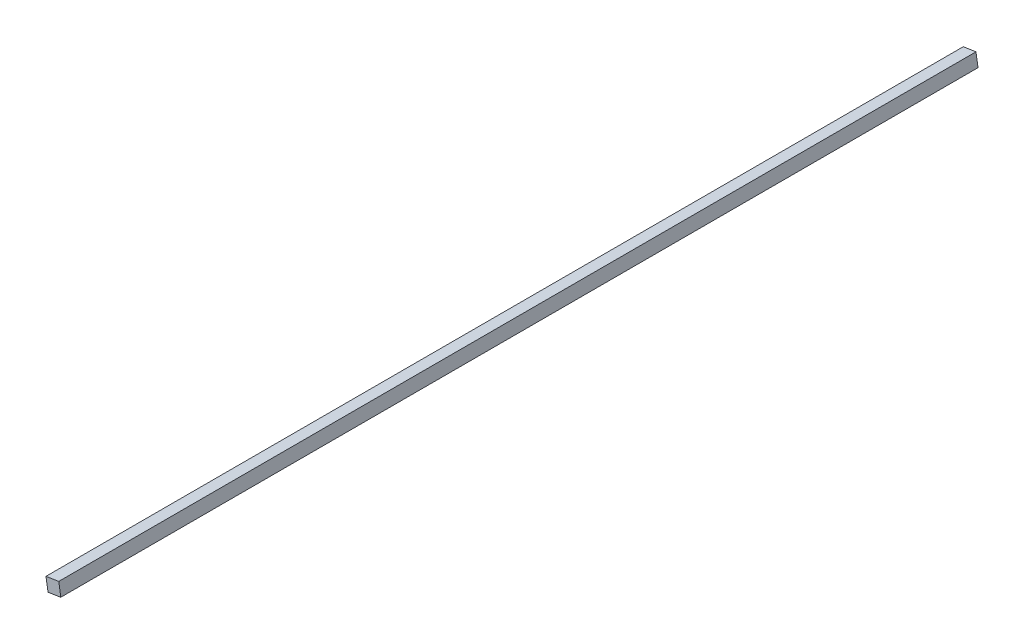
SolidWorks part; units mm, degrees
ref_plane "Front Plane" through (0, 0, 0) normal (0, 0, 1) x (1, 0, 0)
ref_plane "Top Plane" through (0, 0, 0) normal (0, 1, 0) x (1, 0, 0)
ref_plane "Right Plane" through (0, 0, 0) normal (1, 0, 0) x (0, 0, -1)
sketch "Sketch1" plane through (0, 0, 0) normal (0, 0, 1) x (1, 0, 0)
  line L1 (1.6362, -1.1938) -> (1.1938, 1.6362)
  line L2 (1.1938, 1.6362) -> (-1.6362, 1.1938)
  line L3 (-1.6362, 1.1938) -> (-1.1938, -1.6362)
  line L4 (-1.1938, -1.6362) -> (1.6362, -1.1938)
  circle A0 centre (0, 0) radius 1.4322 construction
  dimension "D1" = 2.83
extrude "Boss-Extrude1" add sketch "Sketch1" along normal blind 203.2
